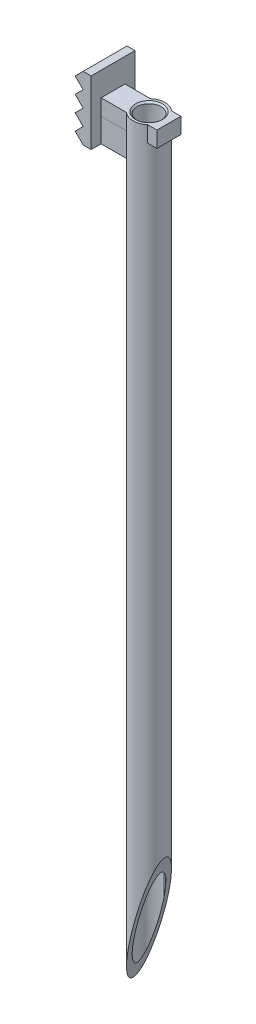
SolidWorks part; units mm, degrees
material "AISI 4340 Steel, normalized"
ref_plane "Front Plane" through (0, 0, 0) normal (0, 0, 1) x (1, 0, 0)
ref_plane "Top Plane" through (0, 0, 0) normal (0, 1, 0) x (1, 0, 0)
ref_plane "Right Plane" through (0, 0, 0) normal (1, 0, 0) x (0, 0, -1)
sketch "Sketch1" plane through (0, 0, 0) normal (0, 0, 1) x (1, 0, 0)
  line L1 (0, 0) -> (3.5, 0)
  line L2 (0, 0) -> (0, 1)
  line L3 (0, 1) -> (3.5, 1)
  line L4 (3.5, 0) -> (3.5, 1)
  dimension "D1" = 1
  dimension "D2" = 3.5
extrude "Boss-Extrude3" add sketch "Sketch1" along normal blind 0.75
sketch "Sketch4" plane through (0, 0, 0) normal (0, -1, 0) x (1, 0, 0)
  line L0 (3.5, 0.75) -> (3.5, 0) construction
  line L2 (0, 0.75) -> (3.5, 0.75) construction
  circle A0 centre (2.255, 0.375) radius 1
  point P4 (3.5, 0.375)
  dimension "D1" = 1.245
  dimension "D3" = 2
  dimension "D2" = 0.375
extrude "Boss-Extrude5" add sketch "Sketch4" along normal blind 46.5 and the other way up to surface (1 mm away) other way up to face at (1.75, 1, 0.375)
sketch "Sketch5" plane through (0, -46.5, 0) normal (0, -1, 0) x (1, 0, 0)
  circle A0 centre (2.255, 0.375) radius 0.75
  dimension "D1" = 1.5
extrude "Cut-Extrude1" cut sketch "Sketch5" against normal blind 18
sketch "Sketch6" plane through (0, 0, 0) normal (-1, 0, 0) x (0, 0, 1)
  line L0 (0.75, 1) -> (0, 1) construction
  line L1 (-1, 2.5) -> (1.75, 2.5)
  line L2 (-1, 2.5) -> (-1, -1.5)
  line L3 (-1, -1.5) -> (1.75, -1.5)
  line L4 (1.75, 2.5) -> (1.75, -1.5)
  line L5 (0.75, 0) -> (0, 0) construction
  line L6 (0, 1) -> (0, 0) construction
  line L7 (0.75, 1) -> (0.75, 0) construction
  dimension "D1" = 1.5
  dimension "D2" = 1.5
  dimension "D3" = 1
  dimension "D4" = 1
extrude "Boss-Extrude6" add sketch "Sketch6" along normal blind 1
sketch "Sketch7" plane through (0, 0, 1.75) normal (0, 0, 1) x (1, 0, 0)
  line L0 (-0.5, 2.5) -> (-1.3576, 2.5)
  line L1 (-0.5, -1.5) -> (-1, -1)
  line L2 (-1, -1.5) -> (0, -1.5) construction
  line L3 (-1, -1) -> (-0.5, -0.5)
  line L4 (-0.5, -0.5) -> (-1, 0)
  line L5 (-1, 0) -> (-0.5, 0.5)
  line L6 (-0.5, 0.5) -> (-1, 1)
  line L7 (-1, 1) -> (-0.5, 1.5)
  line L8 (-0.5, 1.5) -> (-1, 2)
  line L9 (-1, 2) -> (-0.5, 2.5)
  line L10 (-1, 2.5) -> (0, 2.5) construction
  line L11 (-1.3576, 2.5) -> (-1.3576, -1.5)
  line L12 (-1.3576, -1.5) -> (-0.5, -1.5)
extrude "Cut-Extrude2" cut sketch "Sketch7" against normal blind 10
sketch "Sketch8" plane through (0, 0, 0) normal (0, 0, 1) x (1, 0, 0)
  line L0 (1.255, -46.5) -> (3.255, -39)
  line L1 (1.255, -46.5) -> (3.255, -46.5) construction
  line L2 (3.255, -46.5) -> (3.255, 0) construction
  line L3 (3.255, -39) -> (3.255, -46.5)
  line L4 (3.255, -46.5) -> (1.255, -46.5)
  dimension "D1" = 7.5
extrude "Cut-Extrude4" cut sketch "Sketch8" against normal through all both and the other way through all contours L3 L4 L0
sketch "Sketch10" plane through (0, 1, 0) normal (0, 1, 0) x (1, 0, 0)
  circle A0 centre (2.255, -0.375) radius 0.75
  dimension "D1" = 1.5
extrude "Cut-Extrude5" cut sketch "Sketch10" against normal blind 29
sketch "Sketch11" plane through (0, -28, 0) normal (0, 1, 0) x (1, 0, 0)
  circle A0 centre (2.255, -0.375) radius 0.4
  dimension "D1" = 0.8
extrude "Boss-Extrude7" add sketch "Sketch11" along normal blind 1
sketch "Sketch12" plane through (0, -27, 0) normal (0, 1, 0) x (1, 0, 0)
  circle A0 centre (2.255, -0.375) radius 0.325
  dimension "D1" = 0.65
extrude "Cut-Extrude6" cut sketch "Sketch12" against normal blind 35
fillet "Fillet1" radius 0.025 1 edges at (2.255, -27, 0.7)
fillet "Fillet2" radius 0.025 1 edges at (2.255, -27, 0.775)
fillet "Fillet3" radius 0.25 1 edges at (2.255, -28.5, -0.375)
fillet "Fillet4" radius 0.1 1 edges at (2.255, -28.5, 0.05)
ref_point "Point1"
sketch "Sketch13" plane through (0, 0, 0) normal (0, 0, -1) x (-1, 0, 0)
  line L4 (-3.182, 0) -> (-3.182, 1)
  line L5 (-3.182, 1) -> (-3.5, 1)
  line L6 (-3.5, 1) -> (-3.5, 0)
  line L7 (-3.5, 0) -> (-3.182, 0)
  line L8 (-3.182, 0) -> (-3.182, 1)
  line L9 (-3.182, 1) -> (-3.5, 1)
  line L10 (-3.5, 1) -> (-3.5, 0)
  line L11 (-3.5, 0) -> (-3.182, 0)
  dimension "D1" = 0
extrude "Boss-Extrude8" add sketch "Sketch13" along normal blind 0.375
sketch "Sketch14" plane through (0, 0, 0.75) normal (0, 0, 1) x (1, 0, 0)
  line L4 (3.5, 1) -> (3.182, 1)
  line L5 (3.182, 1) -> (3.182, 0)
  line L6 (3.182, 0) -> (3.5, 0)
  line L7 (3.5, 0) -> (3.5, 1)
  line L8 (3.5, 1) -> (3.182, 1)
  line L9 (3.182, 1) -> (3.182, 0)
  line L10 (3.182, 0) -> (3.5, 0)
  line L11 (3.5, 0) -> (3.5, 1)
  dimension "D1" = 0
extrude "Boss-Extrude9" add sketch "Sketch14" along normal blind 0.375
sketch "Sketch15" plane through (3.182, 0, 0) normal (-1, 0, 0) x (0, 0, 1)
  line L4 (0, 0) -> (0, 1)
  line L5 (0, 1) -> (-0.375, 1)
  line L6 (-0.375, 1) -> (-0.375, 0)
  line L7 (-0.375, 0) -> (0, 0)
  line L8 (0, 0) -> (0, 1)
  line L9 (0, 1) -> (-0.375, 1)
  line L10 (-0.375, 1) -> (-0.375, 0)
  line L11 (-0.375, 0) -> (0, 0)
  dimension "D1" = 0
extrude "Boss-Extrude10" add sketch "Sketch15" along normal up to surface (0.2656 mm away)
sketch "Sketch16" plane through (3.182, 0, 0) normal (-1, 0, 0) x (0, 0, 1)
  line L4 (0.75, 1) -> (0.75, 0)
  line L5 (0.75, 0) -> (1.125, 0)
  line L6 (1.125, 0) -> (1.125, 1)
  line L7 (1.125, 1) -> (0.75, 1)
  line L8 (0.75, 1) -> (0.75, 0)
  line L9 (0.75, 0) -> (1.125, 0)
  line L10 (1.125, 0) -> (1.125, 1)
  line L11 (1.125, 1) -> (0.75, 1)
  dimension "D1" = 0
extrude "Boss-Extrude11" add sketch "Sketch16" along normal up to surface (0.2656 mm away)
sketch "Sketch17" plane through (0, 0, 0.75) normal (0, 0, 1) x (1, 0, 0)
  line L4 (0, 0) -> (1.328, 0)
  line L5 (1.328, 0) -> (1.328, 1)
  line L6 (1.328, 1) -> (0, 1)
  line L7 (0, 1) -> (0, 0)
  line L8 (0, 0) -> (1.328, 0)
  line L9 (1.328, 0) -> (1.328, 1)
  line L10 (1.328, 1) -> (0, 1)
  line L11 (0, 1) -> (0, 0)
  dimension "D1" = 0
extrude "Boss-Extrude12" add sketch "Sketch17" along normal up to surface (0.375 mm away) up to face at (3.2082, 0.5, 1.125)
sketch "Sketch18" plane through (1.328, 0, 0) normal (1, 0, 0) x (0, 0, -1)
  line L4 (-1.125, 1) -> (-1.125, 0)
  line L5 (-1.125, 0) -> (-0.75, 0)
  line L6 (-0.75, 0) -> (-0.75, 1)
  line L7 (-0.75, 1) -> (-1.125, 1)
  line L8 (-1.125, 1) -> (-1.125, 0)
  line L9 (-1.125, 0) -> (-0.75, 0)
  line L10 (-0.75, 0) -> (-0.75, 1)
  line L11 (-0.75, 1) -> (-1.125, 1)
  dimension "D1" = 0
extrude "Boss-Extrude13" add sketch "Sketch18" along normal up to surface up to face at (1.255, -46.5, 0.375)
sketch "Sketch19" plane through (0, 0, 0) normal (0, 0, -1) x (-1, 0, 0)
  line L4 (-1.328, 1) -> (-1.328, 0)
  line L5 (-1.328, 0) -> (0, 0)
  line L6 (0, 0) -> (0, 1)
  line L7 (0, 1) -> (-1.328, 1)
  line L8 (-1.328, 1) -> (-1.328, 0)
  line L9 (-1.328, 0) -> (0, 0)
  line L10 (0, 0) -> (0, 1)
  line L11 (0, 1) -> (-1.328, 1)
  dimension "D1" = 0
extrude "Boss-Extrude14" add sketch "Sketch19" along normal up to surface (0.375 mm away) up to face at (3.2082, 0.5, -0.375)
sketch "Sketch20" plane through (1.328, 0, 0) normal (1, 0, 0) x (0, 0, -1)
  line L4 (0.375, 0) -> (0.375, 1)
  line L5 (0.375, 1) -> (0, 1)
  line L6 (0, 1) -> (0, 0)
  line L7 (0, 0) -> (0.375, 0)
  line L8 (0.375, 0) -> (0.375, 1)
  line L9 (0.375, 1) -> (0, 1)
  line L10 (0, 1) -> (0, 0)
  line L11 (0, 0) -> (0.375, 0)
  dimension "D1" = 0
extrude "Boss-Extrude15" add sketch "Sketch20" along normal up to surface up to face at (1.255, -46.5, 0.375)
sketch "Sketch21" plane through (0, 0, 0) normal (0, -1, 0) x (1, 0, 0)
  line L3 (0, 1.125) -> (0, -0.375)
  line L4 (0, -0.375) -> (1.5936, -0.375)
  line L5 (1.5936, 1.125) -> (0, 1.125)
  line L6 (0, 1.125) -> (0, -0.375)
  line L7 (0, -0.375) -> (1.5936, -0.375)
  line L8 (1.5936, 1.125) -> (0, 1.125)
  arc A2 (1.5936, 1.125) -> (1.5936, -0.375) centre (2.255, 0.375) ccw
  arc A4 (1.5936, 1.125) -> (1.5936, -0.375) centre (2.255, 0.375) ccw
  dimension "D1" = 0
extrude "Boss-Extrude16" add sketch "Sketch21" along normal up to surface (1.5 mm away) separate body up to face at (-0.25, -1.5, 0.375)
chamfer "Chamfer1" distance 0.1 angle 45 1 edges at (2.255, 1, 1.125)
